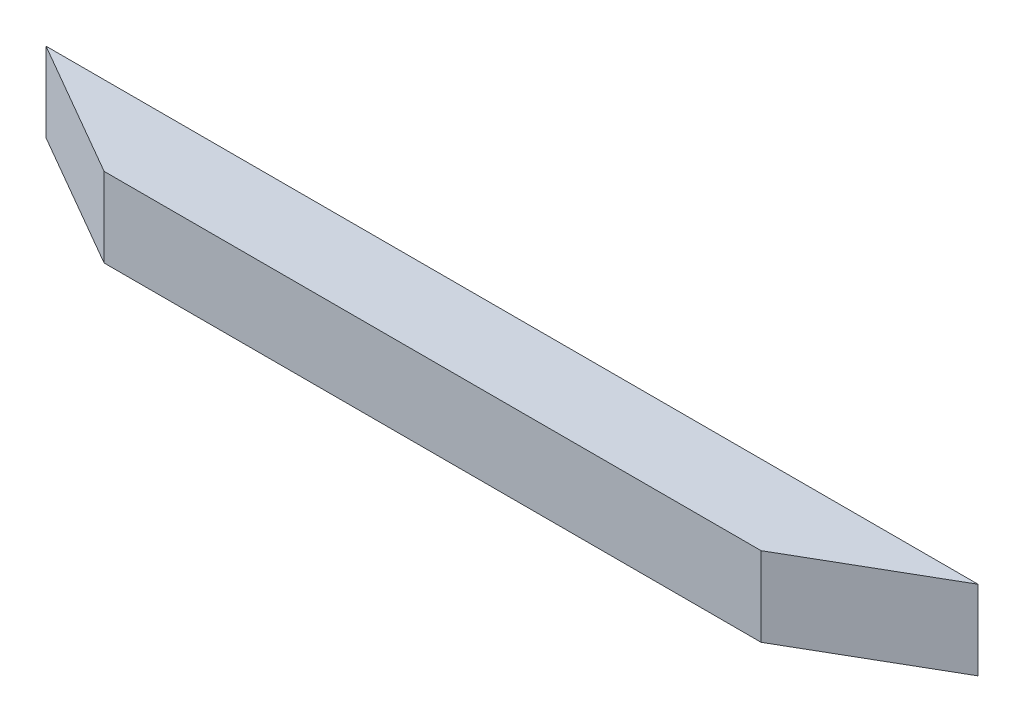
SolidWorks part; units mm, degrees
ref_plane "Front Plane" through (0, 0, 0) normal (0, 0, 1) x (1, 0, 0)
ref_plane "Top Plane" through (0, 0, 0) normal (0, 1, 0) x (1, 0, 0)
ref_plane "Right Plane" through (0, 0, 0) normal (1, 0, 0) x (0, 0, -1)
sketch "Sketch1" plane through (0, 0, 0) normal (0, 1, 0) x (1, 0, 0)
  line L0 (-82.7595, -10) -> (82.7595, -10)
  line L1 (0, 0) -> (100.08, 0) construction
  line L2 (82.7595, -10) -> (117.4005, 10)
  line L3 (117.4005, 10) -> (-117.4005, 10)
  line L4 (0, 27.2438) -> (0, -37.4428) construction
  line L5 (-82.7595, -10) -> (-117.4005, 10)
  point P11 (0, -10)
  point P12 (0, 10)
  dimension "D1" = 10
  dimension "D2" = 10
  dimension "D3" = 100.08
  dimension "D4" = 30
extrude "Boss-Extrude1" add sketch "Sketch1" along normal blind 20
